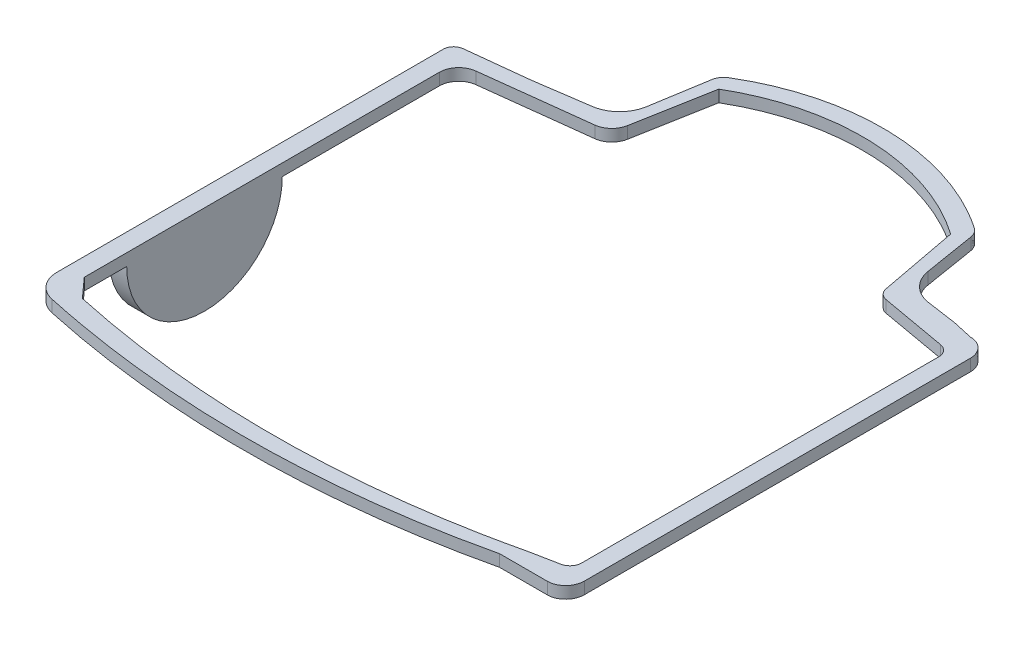
SolidWorks part; units mm, degrees
ref_plane "Front Plane" through (0, 0, 0) normal (0, 0, 1) x (1, 0, 0)
ref_plane "Top Plane" through (0, 0, 0) normal (0, 1, 0) x (1, 0, 0)
ref_plane "Right Plane" through (0, 0, 0) normal (1, 0, 0) x (0, 0, -1)
sketch "Sketch1" plane through (0, 0, 0) normal (0, 1, 0) x (1, 0, 0)
  line L0 (-63.6662, -60.4399) -> (-63.6662, -52.1767)
  line L1 (-68.5882, -50.447) -> (-68.5882, -8.447)
  line L2 (-63.6662, -6.7174) -> (-63.6662, -52.1767)
  line L3 (-68.5882, -50.447) -> (-68.5882, -62.8129)
  line L4 (51.3273, -68.9022) -> (63.5882, -68.9022)
  line L5 (68.5882, -63.7548) -> (68.5882, 35.4422)
  line L6 (63.5882, 40.4689) -> (58.4401, 41.6232)
  line L7 (58.4401, 41.6232) -> (50.5384, 42.7742)
  line L8 (43.7862, 49.4615) -> (41.6482, 62.5408)
  line L9 (-27.295, 64.3172) -> (-29.653, 49.8922)
  line L10 (-36.4052, 43.2049) -> (-49.969, 41.2291)
  line L11 (-50.2387, 41.1946) -> (-65.9185, 39.458)
  line L12 (-68.5882, 36.4763) -> (-68.5882, -8.447)
  line L15 (-63.6662, -6.7174) -> (-63.6662, 30.8625)
  line L16 (-59.2592, 35.8272) -> (-31.9191, 39.093)
  line L17 (-27.5925, 43.165) -> (-23.9873, 63.0324)
  line L18 (38.1031, 60.5724) -> (41.9893, 40.0573)
  line L19 (44.412, 37.6619) -> (61.4351, 34.6371)
  line L20 (63.9103, 31.6834) -> (63.9103, -60.1227)
  line L21 (61.4916, -63.0659) -> (54.2282, -64.5004)
  line L22 (-59.1737, -65.4173) -> (-63.6662, -60.4399)
  arc A0 (-50.2387, 41.1946) -> (-49.969, 41.2291) centre (-51.11, 49.0625) ccw
  arc A1 (-65.9185, 39.458) -> (-68.5882, 36.4763) centre (-65.5882, 36.4763) ccw
  arc A2 (-59.2592, 35.8272) -> (-63.6662, 30.8625) centre (-58.6662, 30.8625) ccw
  arc A3 (-31.9191, 39.093) -> (-27.5925, 43.165) centre (-32.5121, 44.0577) ccw
  arc A4 (41.9893, 40.0573) -> (44.412, 37.6619) centre (44.9369, 40.6157) ccw
  arc A5 (63.9103, 31.6834) -> (61.4351, 34.6371) centre (60.9103, 31.6834) ccw
  arc A6 (61.4916, -63.0659) -> (63.9103, -60.1227) centre (60.9103, -60.1227) ccw
  spline S0 degree 3 poles (-68.5882, -62.8129) (-68.5882, -63.6197) (-68.4563, -64.4041) (-67.928, -65.9279) (-67.5455, -66.626) (-66.5441, -67.8894) (-65.951, -68.4214) (-64.5849, -69.2771) (-63.8468, -69.5788) (-63.0582, -69.7504) knots 0 0 0 0 0.25 0.25 0.5 0.5 0.75 0.75 1 1 1 1
  spline S1 degree 3 poles (-63.0582, -69.7504) (-53.6433, -71.8002) (-44.1436, -73.3197) (-24.9766, -75.311) (-15.3669, -75.7766) (3.9023, -75.6255) (13.4765, -75.0117) (32.4963, -72.7451) (41.944, -71.0926) (51.3273, -68.9022) knots 0 0 0 0 0.25 0.25 0.5 0.5 0.75 0.75 1 1 1 1
  spline S2 degree 3 poles (63.5882, -68.9022) (63.9233, -68.9022) (64.2525, -68.8679) (64.8997, -68.7336) (65.2212, -68.6319) (65.8305, -68.3683) (66.119, -68.2073) (66.6641, -67.8275) (66.9197, -67.6082) (67.3771, -67.1308) (67.5821, -66.8705) (67.9432, -66.3066) (68.0938, -66.0117) (68.3379, -65.3974) (68.4319, -65.0751) (68.5568, -64.4206) (68.5882, -64.0896) (68.5882, -63.7548) knots 0 0 0 0 0.125 0.125 0.25 0.25 0.375 0.375 0.5 0.5 0.625 0.625 0.75 0.75 0.875 0.875 1 1 1 1
  spline S3 degree 3 poles (68.5882, 35.4422) (68.5882, 35.7733) (68.556, 36.0988) (68.4614, 36.5792) (68.422, 36.738) (68.3274, 37.0529) (68.2719, 37.2095) (68.0846, 37.6653) (67.9317, 37.9537) (67.5705, 38.4996) (67.3599, 38.7584) (66.8996, 39.2228) (66.6483, 39.4313) (66.1027, 39.7996) (65.8111, 39.9568) (65.2091, 40.2088) (64.8947, 40.3057) (64.2468, 40.4362) (63.9193, 40.4689) (63.5882, 40.4689) knots 0 0 0 0 0.125 0.125 0.1875 0.1875 0.25 0.25 0.375 0.375 0.5 0.5 0.625 0.625 0.75 0.75 0.875 0.875 1 1 1 1
  spline S4 degree 3 poles (50.5384, 42.7742) (49.6926, 42.8974) (48.8891, 43.1508) (47.7463, 43.7234) (47.3821, 43.9442) (46.698, 44.4366) (46.3759, 44.7092) (45.9235, 45.1583) (45.7775, 45.3152) (45.5009, 45.6373) (45.3696, 45.803) (44.9963, 46.3138) (44.7748, 46.6725) (44.3871, 47.4265) (44.2213, 47.8226) (43.9562, 48.6278) (43.8551, 49.0398) (43.7862, 49.4615) knots 0 0 0 0 0.25 0.25 0.375 0.375 0.5 0.5 0.5625 0.5625 0.625 0.625 0.75 0.75 0.875 0.875 1 1 1 1
  spline S5 degree 3 poles (41.6482, 62.5408) (41.604, 62.811) (41.5334, 63.072) (41.3414, 63.5768) (41.218, 63.823) (40.927, 64.2809) (40.76, 64.4929) (40.3832, 64.8829) (40.1727, 65.0607) (39.9465, 65.2149) knots 0 0 0 0 0.25 0.25 0.5 0.5 0.75 0.75 1 1 1 1
  spline S6 degree 3 poles (39.9465, 65.2149) (37.5483, 66.8487) (35.0632, 68.2927) (29.9253, 70.8149) (27.2725, 71.8932) (23.8496, 73.0077) (23.1596, 73.2188) (21.7688, 73.6173) (21.0668, 73.8049) (18.9605, 74.3275) (17.5515, 74.6238) (13.3103, 75.36) (10.4642, 75.6479) (6.167, 75.7766) (4.73, 75.7688) (1.8463, 75.6495) (0.3952, 75.5373) (-3.9066, 75.0488) (-6.7241, 74.5221) (-12.2608, 73.0778) (-14.9801, 72.1601) (-18.3158, 70.7606) (-18.9804, 70.4677) (-20.2961, 69.8594) (-20.948, 69.5438) (-22.8859, 68.5624) (-24.1541, 67.8622) (-25.3984, 67.116) knots 0 0 0 0 0.125 0.125 0.25 0.25 0.28125 0.28125 0.3125 0.3125 0.375 0.375 0.5 0.5 0.5625 0.5625 0.625 0.625 0.75 0.75 0.875 0.875 0.90625 0.90625 0.9375 0.9375 1 1 1 1
  spline S7 degree 3 poles (-25.3984, 67.116) (-25.6498, 66.9652) (-25.8802, 66.7899) (-26.3006, 66.3922) (-26.4921, 66.1669) (-26.8171, 65.6872) (-26.9528, 65.4317) (-27.1692, 64.8891) (-27.2478, 64.6066) (-27.295, 64.3172) knots 0 0 0 0 0.25 0.25 0.5 0.5 0.75 0.75 1 1 1 1
  spline S8 degree 3 poles (-29.653, 49.8922) (-29.7908, 49.0488) (-30.0542, 48.2484) (-30.6364, 47.112) (-30.8603, 46.7487) (-31.3573, 46.0678) (-31.6315, 45.7477) (-32.0823, 45.2987) (-32.24, 45.1536) (-32.5643, 44.8783) (-32.7311, 44.7478) (-33.2446, 44.3777) (-33.6046, 44.1591) (-34.3606, 43.7788) (-34.7589, 43.6169) (-35.5685, 43.3615) (-35.9823, 43.2665) (-36.4052, 43.2049) knots 0 0 0 0 0.25 0.25 0.375 0.375 0.5 0.5 0.5625 0.5625 0.625 0.625 0.75 0.75 0.875 0.875 1 1 1 1
  spline S9 degree 3 poles (-23.9873, 63.0324) (-22.7971, 63.7292) (-21.5848, 64.3821) (-19.7331, 65.2955) (-19.1103, 65.589) (-17.8537, 66.154) (-17.2191, 66.4258) (-15.9452, 66.9446) (-15.3054, 67.192) (-14.0201, 67.6629) (-13.3746, 67.8864) (-11.4295, 68.5214) (-10.1214, 68.8974) (-7.4829, 69.5563) (-6.1524, 69.8391) (-4.1398, 70.1925) (-3.4661, 70.2985) (-2.4513, 70.4396) (-2.1123, 70.4837) (-1.4329, 70.5659) (-1.0925, 70.604) (-0.4102, 70.6742) (-0.0681, 70.7063) (0.6173, 70.7644) (0.9607, 70.7904) (1.9912, 70.8593) (2.6791, 70.8929) (4.0502, 70.9352) (4.7344, 70.944) (6.1005, 70.9373) (6.7822, 70.9218) (10.1849, 70.7841) (12.8872, 70.4819) (16.2404, 69.8634) (16.9097, 69.7277) (18.246, 69.4317) (18.9129, 69.2714) (20.2441, 68.9262) (20.9094, 68.7409) (22.2274, 68.3482) (22.8811, 68.1405) (24.8265, 67.4844) (26.1026, 67.0028) (28.6137, 65.9522) (29.8486, 65.3832) (33.4923, 63.5466) (35.84, 62.1493) (38.1031, 60.5724) knots 0 0 0 0 0.0625 0.0625 0.09375 0.09375 0.125 0.125 0.15625 0.15625 0.1875 0.1875 0.25 0.25 0.3125 0.3125 0.34375 0.34375 0.359375 0.359375 0.375 0.375 0.390625 0.390625 0.40625 0.40625 0.4375 0.4375 0.46875 0.46875 0.5 0.5 0.625 0.625 0.65625 0.65625 0.6875 0.6875 0.71875 0.71875 0.75 0.75 0.8125 0.8125 0.875 0.875 1 1 1 1
  spline S10 degree 3 poles (54.2282, -64.5004) (53.6469, -64.6361) (53.0654, -64.7704) (52.1928, -64.9692) (51.9019, -65.0349) (51.4654, -65.1328) (51.3199, -65.1653) (51.0288, -65.2299) (50.8833, -65.2621) (50.5922, -65.3262) (50.4466, -65.3581) (50.1554, -65.4217) (50.0098, -65.4534) (49.5729, -65.5479) (49.2816, -65.6105) (48.4075, -65.7965) (47.8245, -65.9184) (44.9081, -66.5178) (42.571, -66.9642) (35.5475, -68.2048) (30.849, -68.9004) (21.4203, -70.0335) (16.69, -70.4709) (9.5705, -70.9299) (7.1933, -71.0501) (2.4307, -71.224) (0.0438, -71.2777) (-7.1183, -71.3386) (-11.8872, -71.2447) (-21.4133, -70.7905) (-26.1719, -70.4301) (-40.4222, -68.9541) (-49.8398, -67.4494) (-59.1737, -65.4173) knots 0 0 0 0 0.015625 0.015625 0.023438 0.023438 0.027344 0.027344 0.03125 0.03125 0.035156 0.035156 0.039062 0.039062 0.046875 0.046875 0.0625 0.0625 0.125 0.125 0.25 0.25 0.375 0.375 0.4375 0.4375 0.5 0.5 0.625 0.625 0.75 0.75 1 1 1 1
extrude "Extrude1" add sketch "Sketch1" along normal blind 3.048
sketch "Sketch4" plane through (0, 3.048, 0) normal (0, 1, 0) x (1, 0, 0)
  line L23 (-68.6924, -50.5281) -> (-68.6924, -8.5281)
sketch "Sketch5" plane through (-68.5882, 0, 0) normal (-1, 0, 0) x (0, 0, 1)
  line L0 (-36.4763, 0) -> (62.8129, 0) construction
  line L2 (9.7355, 2.8728) -> (49.3207, 2.8728)
  arc A0 (9.7355, 2.8728) -> (49.3207, 2.8728) centre (29.5281, 0) ccw
  dimension "D1" = 20
extrude "Extrude2" add sketch "Sketch5" against normal up to vertex
sketch "Sketch7" plane through (0, 3.048, 0) normal (0, 1, 0) x (1, 0, 0)
  line L18 (-68.2882, 36.4763) -> (-68.2882, -62.8129)
  line L19 (51.2928, -68.6022) -> (63.5882, -68.6022)
  line L20 (68.2882, -63.7548) -> (68.2882, 35.4422)
  line L21 (63.555, 40.1689) -> (58.3856, 41.328)
  line L22 (58.3856, 41.328) -> (50.4951, 42.4773)
  line L23 (43.4901, 49.4131) -> (41.3521, 62.4924)
  line L24 (-26.999, 64.2689) -> (-29.3569, 49.8438)
  line L25 (-36.362, 42.908) -> (-49.9257, 40.9323)
  line L26 (-50.2056, 40.8964) -> (-65.8854, 39.1599)
  line L27 (-68.2882, 36.4763) -> (-68.2882, -62.8129)
  line L28 (51.2928, -68.6022) -> (63.5882, -68.6022)
  line L29 (68.2882, -63.7548) -> (68.2882, 35.4422)
  line L30 (63.555, 40.1689) -> (58.3856, 41.328)
  line L31 (58.3856, 41.328) -> (50.4951, 42.4773)
  line L32 (43.4901, 49.4131) -> (41.3521, 62.4924)
  line L33 (-26.999, 64.2689) -> (-29.3569, 49.8438)
  line L34 (-36.362, 42.908) -> (-49.9257, 40.9323)
  line L35 (-50.2056, 40.8964) -> (-65.8854, 39.1599)
  arc A4 (-50.2056, 40.8964) -> (-49.9257, 40.9323) centre (-51.11, 49.0625) ccw
  arc A5 (-65.8854, 39.1599) -> (-68.2882, 36.4763) centre (-65.5882, 36.4763) ccw
  arc A6 (-50.2056, 40.8964) -> (-49.9257, 40.9323) centre (-51.11, 49.0625) ccw
  arc A7 (-65.8854, 39.1599) -> (-68.2882, 36.4763) centre (-65.5882, 36.4763) ccw
  spline S18 degree 3 poles (2845.3766, 643.8871) (964.6517, 253.0383) (-91.253, 2.3128) (-67.6564, -65.7959) (-67.2904, -66.4645) (-66.332, -67.6745) (-65.7641, -68.1842) (-20.4873, -96.5606) (271.1997, 437.5614) (-747.1388, 2817.1171) knots -22.836893 -22.836893 -22.836893 -22.836893 0.25 0.25 0.5 0.5 0.75 0.75 17.811398 17.811398 17.811398 17.811398 only from (-68.2882, -62.8129) to (-62.9944, -69.4573)
  spline S19 degree 3 poles (-711.479, 2803.8939) (-653.2924, 797.0982) (-407.3498, -35.2948) (-24.9451, -75.0124) (-15.3435, -75.4771) (3.9094, -75.3248) (13.4751, -74.7107) (367.1398, -32.5303) (629.5058, 691.0829) (725.5681, 2802.4372) knots -9.48408 -9.48408 -9.48408 -9.48408 0.25 0.25 0.5 0.5 0.75 0.75 9.805368 9.805368 9.805368 9.805368 only from (-62.9944, -69.4573) to (51.2928, -68.6022)
  spline S20 degree 3 poles (-542.1567, 2868.7038) (-65.3638, 287.2972) (31.247, -75.4261) (64.8221, -68.4432) (65.1246, -68.3472) (65.6976, -68.0986) (65.9688, -67.9468) (66.4812, -67.5888) (66.7214, -67.3822) (67.1511, -66.9324) (67.3439, -66.6869) (67.6829, -66.1561) (67.8242, -65.8786) (68.0533, -65.3004) (68.1416, -64.9969) (76.7624, -19.708) (-536.4433, 101.5513) (-2888.5464, 436.1377) knots -13.535591 -13.535591 -13.535591 -13.535591 0.125 0.125 0.25 0.25 0.375 0.375 0.5 0.5 0.625 0.625 0.75 0.75 0.875 0.875 19.140949 19.140949 19.140949 19.140949 only from (63.5882, -68.6022) to (68.2882, -63.7548)
  spline S21 degree 3 poles (-2869.0992, -570.0582) (-298.2991, -97.182) (75.0125, 1.9195) (68.138, 36.667) (68.0475, 36.9676) (67.8108, 37.541) (67.6659, 37.813) (67.3235, 38.3278) (67.124, 38.5717) (66.6879, 39.0088) (66.4499, 39.2048) (65.9328, 39.5507) (65.6571, 39.6977) (65.0873, 39.9327) (64.7893, 40.0227) (38.8341, 45.0872) (-11.2727, -181.468) (301.7381, 3029.8819) knots -14.112891 -14.112891 -14.112891 -14.112891 0.125 0.125 0.25 0.25 0.375 0.375 0.5 0.5 0.625 0.625 0.75 0.75 0.875 0.875 11.348199 11.348199 11.348199 11.348199 only from (68.2882, 35.4422) to (63.555, 40.1689)
  spline S22 degree 3 poles (1153.0725, 2830.2843) (391.9344, 690.8671) (105.5384, 14.4441) (47.5988, 43.4616) (47.2211, 43.6906) (46.5113, 44.2013) (46.1771, 44.4839) (45.7078, 44.9497) (45.5563, 45.1124) (45.2693, 45.4465) (45.133, 45.6183) (44.7457, 46.1481) (44.5159, 46.5201) (44.1136, 47.3022) (43.9416, 47.7131) (26.7055, 100.0401) (514.4938, 302.9936) (2864.9531, 1063.1914) knots -17.95249 -17.95249 -17.95249 -17.95249 0.25 0.25 0.375 0.375 0.5 0.5 0.5625 0.5625 0.625 0.625 0.75 0.75 0.875 0.875 16.412065 16.412065 16.412065 16.412065 only from (50.4951, 42.4773) to (43.4901, 49.4131)
  spline S23 degree 3 poles (-2803.136, -887.8071) (-560.4235, -195.3585) (55.596, 25.3476) (41.0664, 63.4552) (40.9528, 63.681) (40.6853, 64.1018) (40.5295, 64.3) (13.0084, 92.7468) (-421.1981, -348.4642) (-2011.1052, -2123.2383) knots -39.971764 -39.971764 -39.971764 -39.971764 0.25 0.25 0.5 0.5 0.75 0.75 39.729222 39.729222 39.729222 39.729222 only from (41.3521, 62.4924) to (39.7775, 64.9669)
  spline S24 degree 3 poles (-781.9721, -2807.1825) (66.5921, -589.3618) (169.5627, 1.9306) (29.8059, 70.5393) (27.1663, 71.6123) (23.7603, 72.7213) (23.0737, 72.9314) (21.6897, 73.3279) (20.9912, 73.5146) (18.8954, 74.0346) (17.4933, 74.3294) (13.2732, 75.0619) (10.4411, 75.3485) (6.1652, 75.4765) (4.7352, 75.4688) (1.8657, 75.3501) (0.4218, 75.2384) (-3.8586, 74.7523) (-6.6621, 74.2283) (-12.1714, 72.791) (-14.8773, 71.8779) (-18.1966, 70.4852) (-18.8579, 70.1938) (-20.1671, 69.5885) (-20.8158, 69.2745) (-184.675, -13.7084) (32.6624, -832.4156) (838.9306, -2790.2058) knots -6.584072 -6.584072 -6.584072 -6.584072 0.125 0.125 0.25 0.25 0.28125 0.28125 0.3125 0.3125 0.375 0.375 0.5 0.5 0.5625 0.5625 0.625 0.625 0.75 0.75 0.875 0.875 0.90625 0.90625 0.9375 0.9375 8.872905 8.872905 8.872905 8.872905 only from (39.7775, 64.9669) to (-25.2441, 66.8587)
  spline S25 degree 3 poles (1916.9475, -2218.4152) (409.3077, -361.8091) (2.4606, 93.2388) (-26.0827, 66.185) (-26.2574, 65.9786) (-26.557, 65.536) (-26.6845, 65.2955) (-40.3421, 30.9387) (459.0093, -162.7581) (2802.4073, -930.2242) knots -35.904632 -35.904632 -35.904632 -35.904632 0.25 0.25 0.5 0.5 0.75 0.75 34.8303 34.8303 34.8303 34.8303 only from (-25.2441, 66.8587) to (-26.999, 64.2689)
  spline S26 degree 3 poles (-2791.3865, 1214.9974) (-789.1674, 454.8997) (1.9353, 110.0136) (-30.2765, 47.1565) (-30.3856, 46.963) (-30.6163, 46.5886) (-30.7385, 46.4067) (-31.1252, 45.877) (-31.4097, 45.545) (-31.8775, 45.0793) (-32.0411, 44.9289) (-32.3776, 44.6434) (-32.5505, 44.5081) (-33.0833, 44.1243) (-33.4568, 43.8976) (-34.241, 43.5032) (-34.6542, 43.3353) (-86.0044, 27.1439) (-273.6151, 509.1391) (-981.8306, 2888.1835) knots -19.685353 -19.685353 -19.685353 -19.685353 0.25 0.25 0.3125 0.3125 0.375 0.375 0.5 0.5 0.5625 0.5625 0.625 0.625 0.75 0.75 0.875 0.875 16.035423 16.035423 16.035423 16.035423 only from (-29.3569, 49.8438) to (-36.362, 42.908)
  spline S27 degree 3 poles (-68.2882, -62.8129) (-68.2882, -63.5855) (-68.162, -64.3366) (-67.6564, -65.7959) (-67.2904, -66.4645) (-66.332, -67.6745) (-65.7641, -68.1842) (-64.4564, -69.0038) (-63.7495, -69.2929) (-62.9944, -69.4573) knots 0 0 0 0 0.25 0.25 0.5 0.5 0.75 0.75 1 1 1 1
  spline S28 degree 3 poles (-62.9944, -69.4573) (-53.5875, -71.5053) (-44.0958, -73.0233) (-24.9451, -75.0124) (-15.3435, -75.4771) (3.9094, -75.3248) (13.4751, -74.7107) (32.4783, -72.4442) (41.9176, -70.7907) (51.2928, -68.6022) knots 0 0 0 0 0.25 0.25 0.5 0.5 0.75 0.75 1 1 1 1
  spline S29 degree 3 poles (63.5882, -68.6022) (63.9035, -68.6022) (64.2133, -68.5698) (64.8221, -68.4432) (65.1246, -68.3472) (65.6976, -68.0986) (65.9688, -67.9468) (66.4812, -67.5888) (66.7214, -67.3822) (67.1511, -66.9324) (67.3439, -66.6869) (67.6829, -66.1561) (67.8242, -65.8786) (68.0533, -65.3004) (68.1416, -64.9969) (68.2587, -64.3812) (68.2882, -64.0698) (68.2882, -63.7548) knots 0 0 0 0 0.125 0.125 0.25 0.25 0.375 0.375 0.5 0.5 0.625 0.625 0.75 0.75 0.875 0.875 1 1 1 1
  spline S30 degree 3 poles (68.2882, 35.4422) (68.2882, 35.7548) (68.2577, 36.0622) (68.138, 36.667) (68.0475, 36.9676) (67.8108, 37.541) (67.6659, 37.813) (67.3235, 38.3278) (67.124, 38.5717) (66.6879, 39.0088) (66.4499, 39.2048) (65.9328, 39.5507) (65.6571, 39.6977) (65.0873, 39.9327) (64.7893, 40.0227) (64.1771, 40.1422) (63.8674, 40.1689) (63.555, 40.1689) knots 0 0 0 0 0.125 0.125 0.25 0.25 0.375 0.375 0.5 0.5 0.625 0.625 0.75 0.75 0.875 0.875 1 1 1 1
  spline S31 degree 3 poles (50.4951, 42.4773) (49.6178, 42.6051) (48.7843, 42.8679) (47.5988, 43.4616) (47.2211, 43.6906) (46.5113, 44.2013) (46.1771, 44.4839) (45.7078, 44.9497) (45.5563, 45.1124) (45.2693, 45.4465) (45.133, 45.6183) (44.7457, 46.1481) (44.5159, 46.5201) (44.1136, 47.3022) (43.9416, 47.7131) (43.6665, 48.5483) (43.5616, 48.9757) (43.4901, 49.4131) knots 0 0 0 0 0.25 0.25 0.375 0.375 0.5 0.5 0.5625 0.5625 0.625 0.625 0.75 0.75 0.875 0.875 1 1 1 1
  spline S32 degree 3 poles (41.3521, 62.4924) (41.3113, 62.742) (41.2459, 62.9845) (41.0664, 63.4552) (40.9528, 63.681) (40.6853, 64.1018) (40.5295, 64.3) (40.1787, 64.6625) (39.9866, 64.8245) (39.7775, 64.9669) knots 0 0 0 0 0.25 0.25 0.5 0.5 0.75 0.75 1 1 1 1
  spline S33 degree 3 poles (39.7775, 64.9669) (37.3913, 66.5927) (34.9184, 68.0295) (29.8059, 70.5393) (27.1663, 71.6123) (23.7603, 72.7213) (23.0737, 72.9314) (21.6897, 73.3279) (20.9912, 73.5146) (18.8954, 74.0346) (17.4933, 74.3294) (13.2732, 75.0619) (10.4411, 75.3485) (6.1652, 75.4765) (4.7352, 75.4688) (1.8657, 75.3501) (0.4218, 75.2384) (-3.8586, 74.7523) (-6.6621, 74.2283) (-12.1714, 72.791) (-14.8773, 71.8779) (-18.1966, 70.4852) (-18.8579, 70.1938) (-20.1671, 69.5885) (-20.8158, 69.2745) (-22.744, 68.2979) (-24.0059, 67.6013) (-25.2441, 66.8587) knots 0 0 0 0 0.125 0.125 0.25 0.25 0.28125 0.28125 0.3125 0.3125 0.375 0.375 0.5 0.5 0.5625 0.5625 0.625 0.625 0.75 0.75 0.875 0.875 0.90625 0.90625 0.9375 0.9375 1 1 1 1
  spline S34 degree 3 poles (-25.2441, 66.8587) (-25.4766, 66.7193) (-25.6907, 66.5566) (-26.0827, 66.185) (-26.2574, 65.9786) (-26.557, 65.536) (-26.6845, 65.2955) (-26.8834, 64.7952) (-26.9552, 64.5364) (-26.999, 64.2689) knots 0 0 0 0 0.25 0.25 0.5 0.5 0.75 0.75 1 1 1 1
  spline S35 degree 3 poles (-29.3569, 49.8438) (-29.4999, 48.969) (-29.7731, 48.1388) (-30.2765, 47.1565) (-30.3856, 46.963) (-30.6163, 46.5886) (-30.7385, 46.4067) (-31.1252, 45.877) (-31.4097, 45.545) (-31.8775, 45.0793) (-32.0411, 44.9289) (-32.3776, 44.6434) (-32.5505, 44.5081) (-33.0833, 44.1243) (-33.4568, 43.8976) (-34.241, 43.5032) (-34.6542, 43.3353) (-35.494, 43.0705) (-35.9232, 42.9719) (-36.362, 42.908) knots 0 0 0 0 0.25 0.25 0.3125 0.3125 0.375 0.375 0.5 0.5 0.5625 0.5625 0.625 0.625 0.75 0.75 0.875 0.875 1 1 1 1
  dimension "D1" = 0.3
extrude "Extrude3" cut sketch "Sketch7" against normal blind 66 flip side to cut
